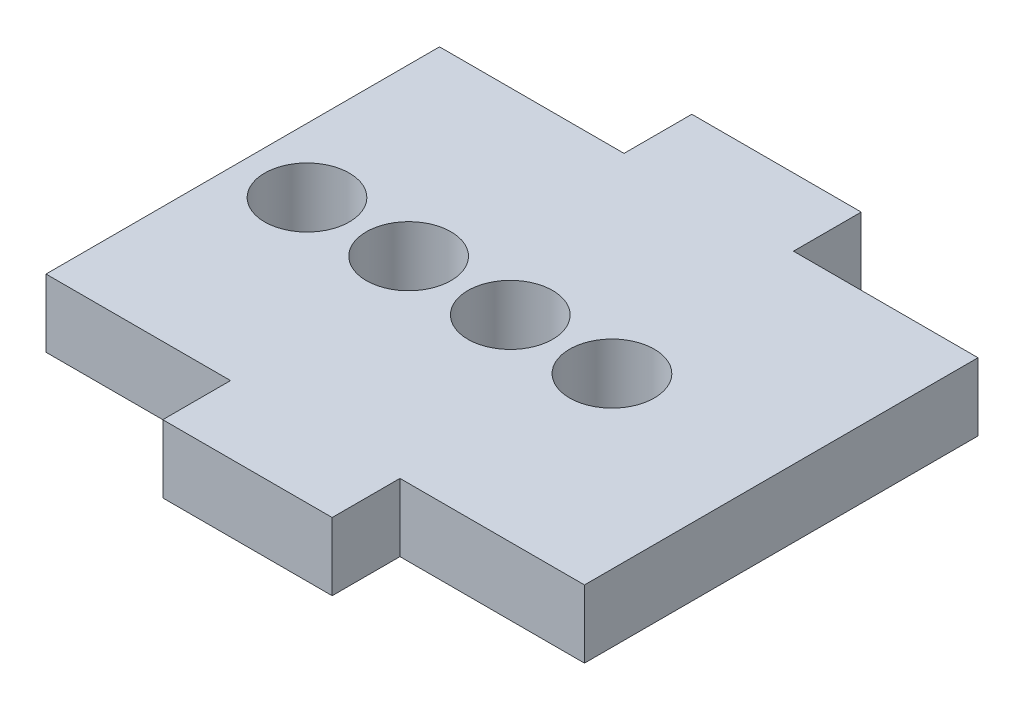
SolidWorks part; units mm, degrees
ref_plane "Front Plane" through (0, 0, 0) normal (0, 0, 1) x (1, 0, 0)
ref_plane "Top Plane" through (0, 0, 0) normal (0, 1, 0) x (1, 0, 0)
ref_plane "Right Plane" through (0, 0, 0) normal (1, 0, 0) x (0, 0, -1)
sketch "Sketch1" plane through (0, 0, 0) normal (0, 1, 0) x (1, 0, 0)
  line L0 (36.7869, 11.6138) -> (44.4925, 11.6138)
  line L1 (27.5186, 11.6138) -> (12.7082, 11.6138)
  line L2 (27.5186, -11.6138) -> (12.7082, -11.6138)
  line L3 (0, 0) -> (46.96, 0) construction
  line L4 (36.7869, -11.6138) -> (44.4925, -11.6138)
  line L5 (44.4925, 11.6138) -> (44.4925, -11.6138)
  line L10 (27.5186, 11.6138) -> (36.7869, 11.6138)
  line L11 (12.7082, 11.6138) -> (12.7082, -11.6138)
  line L15 (27.5186, -11.6138) -> (36.7869, -11.6138)
  circle A15 centre (16.5, 0) radius 2.5
  circle A16 centre (22.5, 0) radius 2.5
  circle A17 centre (28.5, 0) radius 2.5
  circle A18 centre (34.5, 0) radius 2.5
extrude "Boss-Extrude2" add sketch "Sketch1" along normal blind 4
sketch "Sketch13" plane through (0, 4, 0) normal (0, 1, 0) x (1, 0, 0)
  line L0 (16.5, 0) -> (34.5, 0) construction
sketch "Sketch14" plane through (0, 0, 11.6138) normal (0, 0, 1) x (1, 0, 0)
  line L0 (12.7082, 2) -> (44.4925, 2) construction
  line L1 (12.7082, 4) -> (12.7082, 0) construction
  line L2 (44.4925, 4) -> (44.4925, 0) construction
  line L3 (12.7082, 4) -> (44.4925, 4) construction
  line L4 (23.6003, 0) -> (33.6003, 0)
  line L5 (23.6003, 0) -> (23.6003, 4)
  line L6 (23.6003, 4) -> (33.6003, 4)
  line L7 (33.6003, 0) -> (33.6003, 4)
  line L8 (23.6003, 0) -> (33.6003, 4) construction
  line L9 (23.6003, 4) -> (33.6003, 0) construction
  point P6 (28.6003, 2)
  dimension "D1" = 10
extrude "Boss-Extrude5" add sketch "Sketch14" along normal blind 4
sketch "Sketch5" plane through (0, 0, 0) normal (0, -1, 0) x (1, 0, 0)
  line L0 (16.5, 0) -> (34.5, 0)
  circle A3 centre (16.5, 0) radius 2.5
  circle A4 centre (22.5, 0) radius 2.5
  circle A5 centre (28.5, 0) radius 2.5
  circle A6 centre (34.5, 0) radius 2.5
  dimension "D2" = 4
sketch "Sketch15" plane through (0, 0, -11.6138) normal (0, 0, -1) x (-1, 0, 0)
  line L0 (-23.6003, 4) -> (-23.6003, 0) construction
  line L1 (-23.6003, 0) -> (-33.6003, 0)
  line L2 (-23.6003, 0) -> (-23.6003, 4)
  line L3 (-23.6003, 4) -> (-33.6003, 4)
  line L4 (-33.6003, 0) -> (-33.6003, 4)
extrude "Boss-Extrude6" add sketch "Sketch15" along normal blind 4 contours L2 L3 L4 L1
